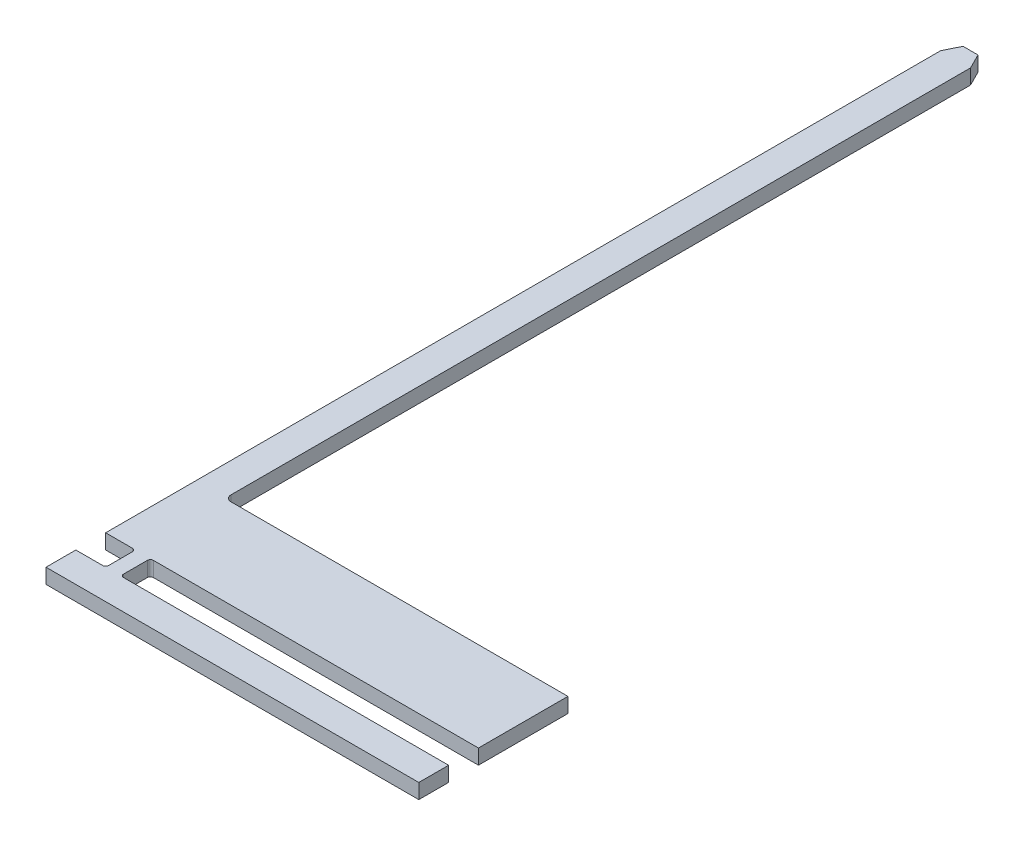
SolidWorks part; units mm, degrees
ref_plane "Front" through (0, 0, 0) normal (0, 0, 1) x (1, 0, 0)
ref_plane "Top" through (0, 0, 0) normal (0, 1, 0) x (1, 0, 0)
ref_plane "Right" through (0, 0, 0) normal (1, 0, 0) x (0, 0, -1)
sketch "Sketch1" plane through (0, 0, 0) normal (0, 1, 0) x (1, 0, 0)
  line L0 (-0.1752, 0.4548) -> (-0.1802, 0.4648)
  line L1 (0.0548, -0.1252) -> (-0.1632, -0.1252)
  line L2 (0.0548, -0.1252) -> (0.0548, -0.1452)
  line L3 (0.0548, -0.1452) -> (-0.1952, -0.1452)
  line L4 (-0.1952, -0.1252) -> (-0.1952, -0.1452)
  line L6 (-0.1652, -0.1232) -> (-0.1652, -0.1072)
  line L8 (-0.1752, -0.1232) -> (-0.1752, -0.1072)
  line L9 (-0.1712, -0.0452) -> (0.0548, -0.0452)
  line L10 (-0.1952, -0.0652) -> (-0.1952, -0.1052)
  line L11 (-0.1952, -0.1052) -> (-0.1772, -0.1052)
  line L12 (0.0548, -0.0452) -> (0.0548, -0.1052)
  line L14 (-0.1952, -0.0652) -> (-0.1952, 0.4548)
  line L16 (-0.1752, -0.0412) -> (-0.1752, 0.4548)
  line L17 (-0.1802, 0.4648) -> (-0.1902, 0.4648)
  line L18 (-0.1902, 0.4648) -> (-0.1952, 0.4548)
  line L19 (-0.1632, -0.1052) -> (0.0548, -0.1052)
  line L20 (-0.1772, -0.1252) -> (-0.1952, -0.1252)
  arc A0 (-0.1632, -0.1252) -> (-0.1652, -0.1232) centre (-0.1632, -0.1232) cw
  arc A1 (-0.1772, -0.1252) -> (-0.1752, -0.1232) centre (-0.1772, -0.1232) ccw
  arc A2 (-0.1772, -0.1052) -> (-0.1752, -0.1072) centre (-0.1772, -0.1072) cw
  arc A3 (-0.1632, -0.1052) -> (-0.1652, -0.1072) centre (-0.1632, -0.1072) ccw
  arc A4 (-0.1712, -0.0452) -> (-0.1752, -0.0412) centre (-0.1712, -0.0412) cw
  point P29 (-0.1752, -0.1052)
  point P34 (-0.1752, -0.0452)
  dimension "D10" = 0.002
  dimension "D11" = 0.004
  dimension "D1" = 0.02
  dimension "D2" = 0.06
  dimension "D3" = 0.02
  dimension "D4" = 0.01
  dimension "D5" = 0.02
  dimension "D6" = 0.01
  dimension "D7" = 0.01
  dimension "D8" = 0.5
  dimension "D9" = 0.25
extrude "Boss-Extrude1" add sketch "Sketch1" along normal blind 0.01
